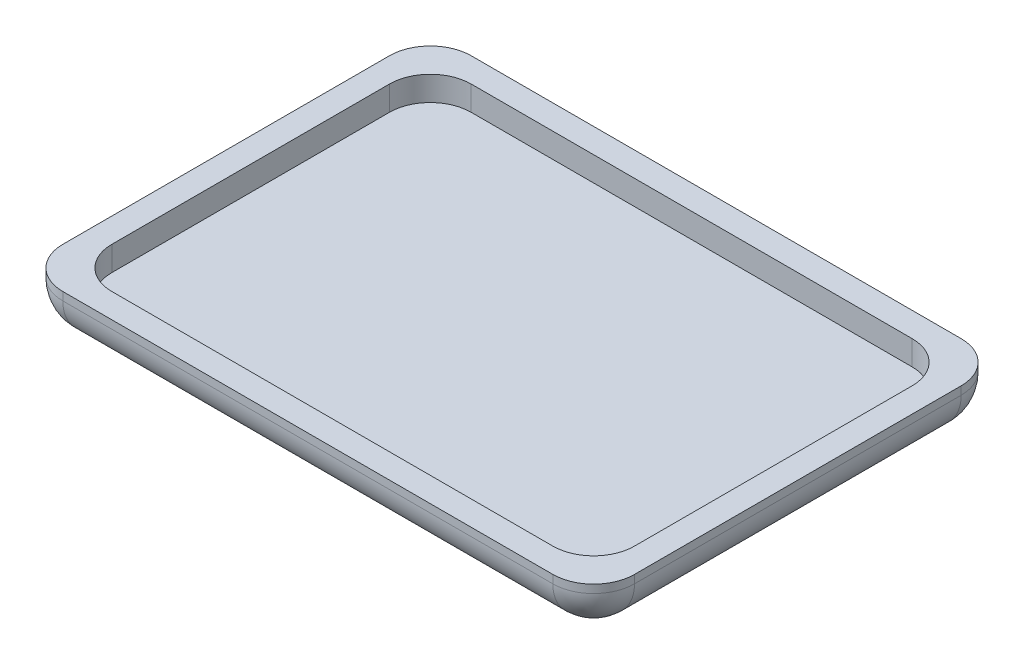
SolidWorks part; units mm, degrees
ref_plane "Front Plane" through (0, 0, 0) normal (0, 0, 1) x (1, 0, 0)
ref_plane "Top Plane" through (0, 0, 0) normal (0, 1, 0) x (1, 0, 0)
ref_plane "Right Plane" through (0, 0, 0) normal (1, 0, 0) x (0, 0, -1)
sketch "Sketch1" plane through (0, 0, 0) normal (0, 1, 0) x (1, 0, 0)
  line L1 (-35, 25) -> (35, 25)
  line L2 (-35, 25) -> (-35, -25)
  line L3 (-35, -25) -> (35, -25)
  line L4 (35, 25) -> (35, -25)
  line L5 (-35, 25) -> (35, -25) construction
  line L6 (-35, -25) -> (35, 25) construction
  point P0 (0, 0)
  dimension "D1" = 70
  dimension "D2" = 50
extrude "Boss-Extrude1" add sketch "Sketch1" along normal blind 6
shell "Shell1" thickness 3
fillet "Fillet1" radius 5 1 edges at (35, 3, 25)
fillet "Fillet2" radius 5 1 edges at (35, 3, -25)
fillet "Fillet3" radius 5 1 edges at (-35, 3, 25)
fillet "Fillet4" radius 5 1 edges at (-35, 3, -25)
fillet "Fillet5" radius 5 8 edges at (35, 0, 0) (33.5355, 0, 23.5355) (0, 0, -25) (33.5355, 0, -23.5355) (0, 0, 25) (-33.5355, 0, 23.5355) (-35, 0, 0) (-33.5355, 0, -23.5355)
fillet "Fillet6" radius 5 1 edges at (32, 4.5, 22)
fillet "Fillet7" radius 5 1 edges at (-32, 4.5, 22)
fillet "Fillet8" radius 5 1 edges at (-32, 4.5, -22)
fillet "Fillet9" radius 5 1 edges at (32, 4.5, -22)
